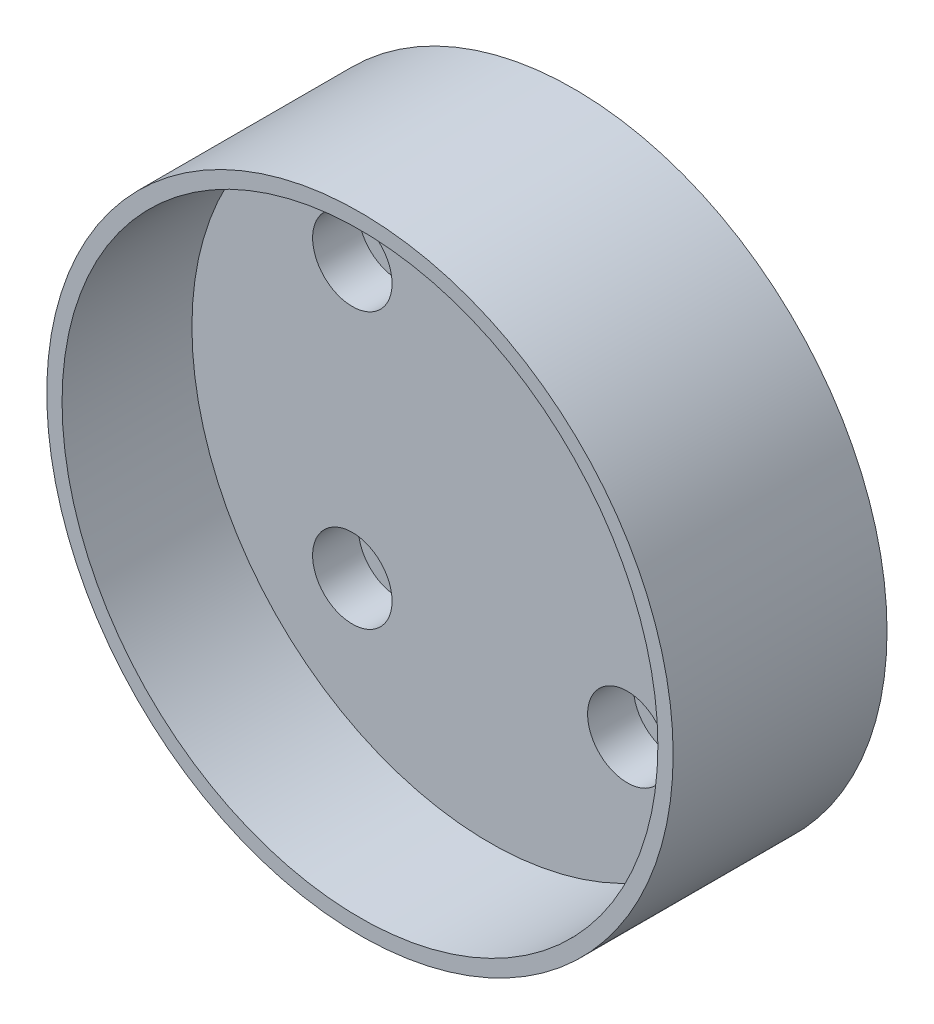
SolidWorks part; units mm, degrees
ref_plane "Piano frontale" through (0, 0, 0) normal (0, 0, 1) x (1, 0, 0)
ref_plane "Piano superiore" through (0, 0, 0) normal (0, 1, 0) x (1, 0, 0)
ref_plane "Piano destro" through (0, 0, 0) normal (1, 0, 0) x (0, 0, -1)
sketch "Schizzo2" plane through (0, 0, 0) normal (0, 0, 1) x (1, 0, 0)
  circle A0 centre (0, 0) radius 41
  dimension "D1" = 82
extrude "Estrusione-Estrusione1" add sketch "Schizzo2" along normal blind 28 contours A0
sketch "Schizzo3" plane through (0, 0, 28) normal (0, 0, 1) x (1, 0, 0)
  circle A0 centre (0, 0) radius 39
  dimension "D1" = 78
extrude "Taglio-Estrusione1" cut sketch "Schizzo3" against normal blind 17
sketch "Schizzo4" plane through (0, 0, 0) normal (0, 0, -1) x (-1, 0, 0)
  line L1 (-18, -18) -> (18, -18)
  line L2 (-18, -18) -> (-18, 18)
  line L3 (-18, 18) -> (18, 18)
  line L4 (18, -18) -> (18, 18)
  line L5 (-18, -18) -> (18, 18) construction
  line L6 (-18, 18) -> (18, -18) construction
  circle A0 centre (-18, 18) radius 2.75
  circle A1 centre (18, 18) radius 2.75
  circle A2 centre (18, -18) radius 2.75
  circle A3 centre (-18, -18) radius 2.75
  point P0 (0, 0)
  dimension "D3" = 5.5
  dimension "D4" = 5.5
  dimension "D5" = 5.5
  dimension "D6" = 5.5
  dimension "D1" = 36
  dimension "D2" = 36
extrude "Taglio-Estrusione3" cut sketch "Schizzo4" against normal through all contours A3 | A2 | A1 | A0
sketch "Schizzo5" plane through (0, 0, 11) normal (0, 0, 1) x (1, 0, 0)
  circle A0 centre (-18, 18) radius 5.2
  circle A1 centre (18, 18) radius 5.2
  circle A2 centre (18, -18) radius 5.2
  circle A3 centre (-18, -18) radius 5.2
  dimension "D1" = 10.4
  dimension "D2" = 10.4
  dimension "D3" = 10.4
  dimension "D4" = 10.4
extrude "Taglio-Estrusione4" cut sketch "Schizzo5" against normal blind 6
